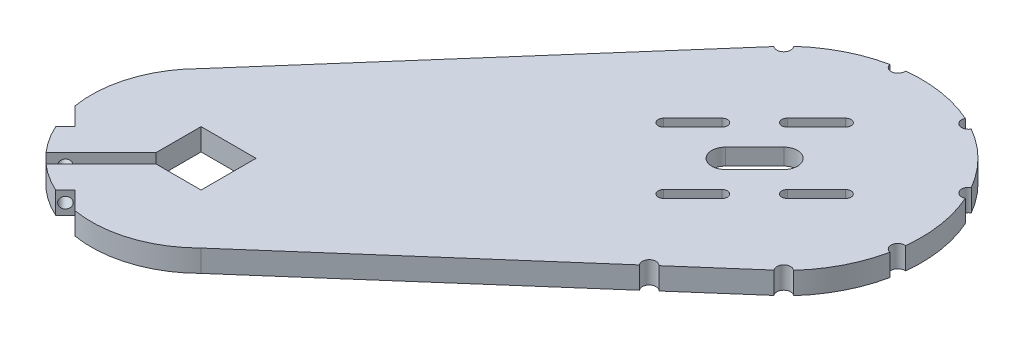
SolidWorks part; units mm, degrees
material "1060-H12"
ref_plane "Plan de face" through (0, 0, 0) normal (0, 0, 1) x (1, 0, 0)
ref_plane "Plan de dessus" through (0, 0, 0) normal (0, 1, 0) x (1, 0, 0)
ref_plane "Plan de droite" through (0, 0, 0) normal (1, 0, 0) x (0, 0, -1)
sketch "Esquisse1" plane through (0, 0, 0) normal (0, 1, 0) x (1, 0, 0)
  line L0 (0, 0) -> (106.066, 106.066) construction
  line L1 (-10, 10) -> (10, 10)
  line L2 (-10, 10) -> (-10, -10)
  line L3 (-10, -10) -> (10, -10)
  line L4 (10, 10) -> (10, -10)
  line L5 (-10, 10) -> (10, -10) construction
  line L6 (-10, -10) -> (10, 10) construction
  line L7 (106.066, 106.066) -> (141.4214, 70.7107) construction
  line L8 (0, 0) -> (28.2843, -28.2843) construction
  line L9 (28.2843, -28.2843) -> (141.4214, 70.7107)
  line L10 (-28.2843, 28.2843) -> (70.7107, 141.4214)
  arc A0 (70.7107, 141.4214) -> (141.4214, 70.7107) centre (106.066, 106.066) cw
  arc A1 (-28.2843, 28.2843) -> (28.2843, -28.2843) centre (0, 0) ccw
  dimension "D3" = 150
  dimension "D1" = 20
  dimension "D4" = 50
  dimension "D2" = 20
  dimension "D5" = 40
extrude "Boss.-Extru.1" add sketch "Esquisse1" along normal blind 8 contours L10 A1 L9 A0 L1 L4 L3 L2
sketch "Esquisse3" plane through (0, 8, 0) normal (0, 1, 0) x (1, 0, 0)
  line L0 (-10, -10) -> (-28.5289, -28.5289) construction
  line L3 (-8.2322, -11.7678) -> (-27.2344, -30.7699)
  line L4 (-27.2344, -30.7699) -> (-30.7699, -27.2344)
  line L5 (-30.7699, -27.2344) -> (-11.7678, -8.2322)
  line L6 (-11.7678, -8.2322) -> (-9.7269, -6.1913)
  line L7 (-9.7269, -6.1913) -> (-6.1913, -9.7269)
  line L8 (-6.1913, -9.7269) -> (-8.2322, -11.7678)
  line L9 (-8.2322, -11.7678) -> (-8.2082, -11.7266)
  point P3 (-19.2631, -19.2631)
  dimension "D1" = 13.1
  dimension "D2" = 2.5
  dimension "D3" = 2.5
extrude "Enlèv. mat.-Extru.1" cut sketch "Esquisse3" against normal through all
ref_plane "Plan1" through (0, 0, 0) normal (0.7071, 0, 0.7071) x (0.7071, 0, -0.7071)
sketch "Esquisse4" plane through (1.7678, 0, 1.7678) normal (-0.7071, 0, -0.7071) x (-0.7071, 0, 0.7071)
  line L0 (11.6421, 8) -> (39.9218, 8) construction
  line L1 (39.9218, 0) -> (39.9218, 8) construction
  circle A0 centre (34.9218, 4) radius 2
  point P0 (34.9218, 4)
  point P5 (39.9218, 4)
  dimension "D1" = 4
  dimension "D2" = 5
extrude "Enlèv. mat.-Extru.2" cut sketch "Esquisse4" against normal through all and the other way through all
sketch "Esquisse5" plane through (0, 8, 0) normal (0, 1, 0) x (1, 0, 0)
  line L0 (-29.9967, -26.4612) -> (-26.4612, -22.9257) construction
  line L1 (-29.9967, -26.4612) -> (-10, -6.4645) construction
  line L2 (-26.4612, -22.9257) -> (-41.741, -7.6459) construction
  line L3 (-34.6837, -14.7032) -> (-36.4514, -16.471)
  line L4 (-36.4514, -16.471) -> (-40.9085, -7.7776)
  line L5 (-40.9085, -7.7776) -> (-39.4911, -6.3602)
  line L6 (-39.4911, -6.3602) -> (-32.9159, -12.9355)
  line L7 (-32.9159, -12.9355) -> (-34.6837, -14.7032)
  line L8 (-28.8576, -28.8576) -> (-15.8397, -15.8397) construction
  line L9 (-3.1113, -3.1113) -> (3.1113, 3.1113) construction
  line L10 (-7.7776, -40.9085) -> (-6.3602, -39.4911)
  line L11 (-16.471, -36.4514) -> (-7.7776, -40.9085)
  line L12 (-14.7032, -34.6837) -> (-16.471, -36.4514)
  line L13 (-12.9355, -32.9159) -> (-14.7032, -34.6837)
  line L14 (-6.3602, -39.4911) -> (-12.9355, -32.9159)
  arc A0 (-28.2843, 28.2843) -> (-29.9967, -26.4612) centre (0, 0) ccw construction
  dimension "D1" = 5
  dimension "D2" = 2.5
  dimension "D3" = 2.5
extrude "Enlèv. mat.-Extru.3" cut sketch "Esquisse5" against normal through all
sketch "Esquisse7" plane through (0, 8, 0) normal (0, 1, 0) x (1, 0, 0)
  line L0 (0, 0) -> (106.066, 106.066) construction
  line L1 (106.066, 106.066) -> (141.4214, 70.7107) construction
  line L2 (10, 10) -> (106.066, 106.066) construction
  line L6 (106.066, 106.066) -> (109.6016, 109.6016) construction
  line L7 (95.4594, 95.4594) -> (66.5612, 95.4594) construction
  line L8 (95.4594, 95.4594) -> (106.066, 106.066) construction
  line L9 (91.9239, 98.9949) -> (102.5305, 109.6016)
  line L10 (98.9949, 91.9239) -> (109.6016, 102.5305)
  line L11 (106.066, 106.066) -> (106.066, 143.8436) construction
  line L12 (95.4594, 95.4594) -> (95.4594, 136.3981) construction
  line L13 (106.066, 106.066) -> (72.9746, 106.066) construction
  line L26 (95.4594, 117.9594) -> (106.066, 128.566) construction
  line L27 (94.0452, 119.3736) -> (104.6518, 129.9802)
  line L28 (96.8736, 116.5452) -> (107.4802, 127.1518)
  line L29 (72.9594, 95.4594) -> (83.566, 106.066) construction
  line L30 (71.5452, 96.8736) -> (82.1518, 107.4802)
  line L31 (74.3736, 94.0452) -> (84.9802, 104.6518)
  line L32 (117.9594, 95.4594) -> (128.566, 106.066) construction
  line L33 (119.3736, 94.0452) -> (129.9802, 104.6518)
  line L34 (116.5452, 96.8736) -> (127.1518, 107.4802)
  line L35 (95.4594, 72.9594) -> (106.066, 83.566) construction
  line L36 (96.8736, 71.5452) -> (107.4802, 82.1518)
  line L37 (94.0452, 74.3736) -> (104.6518, 84.9802)
  arc A0 (91.9239, 98.9949) -> (98.9949, 91.9239) centre (95.4594, 95.4594) ccw
  arc A1 (109.6016, 102.5305) -> (102.5305, 109.6016) centre (106.066, 106.066) ccw
  arc A10 (94.0452, 119.3736) -> (96.8736, 116.5452) centre (95.4594, 117.9594) ccw
  arc A11 (107.4802, 127.1518) -> (104.6518, 129.9802) centre (106.066, 128.566) ccw
  arc A12 (71.5452, 96.8736) -> (74.3736, 94.0452) centre (72.9594, 95.4594) ccw
  arc A13 (84.9802, 104.6518) -> (82.1518, 107.4802) centre (83.566, 106.066) ccw
  arc A14 (119.3736, 94.0452) -> (116.5452, 96.8736) centre (117.9594, 95.4594) cw
  arc A15 (127.1518, 107.4802) -> (129.9802, 104.6518) centre (128.566, 106.066) cw
  arc A16 (96.8736, 71.5452) -> (94.0452, 74.3736) centre (95.4594, 72.9594) cw
  arc A17 (104.6518, 84.9802) -> (107.4802, 82.1518) centre (106.066, 83.566) cw
  point P0 (106.066, 106.066)
  point P8 (95.4594, 95.4594)
  point P13 (100.7627, 100.7627)
  point P21 (106.066, 121.066)
  point P24 (95.4594, 110.4594)
  point P25 (91.066, 106.066)
  point P26 (80.4594, 95.4594)
  point P55 (106.066, 128.566)
  point P56 (95.4594, 117.9594)
  point P57 (83.566, 106.066)
  point P58 (72.9594, 95.4594)
  point P59 (100.7627, 123.2627)
  point P68 (78.2627, 100.7627)
  point P75 (123.2627, 100.7627)
  point P82 (100.7627, 78.2627)
  dimension "D4" = 45
  dimension "D11" = 15
  dimension "D1" = 5
  dimension "D2" = 15
  dimension "D3" = 45
  dimension "D5" = 45
  dimension "D6" = 45
  dimension "D7" = 15
  dimension "D8" = 15
  dimension "D9" = 15
  dimension "D10" = 15
  dimension "D12" = 22.5
  dimension "D13" = 22.5
  dimension "D14" = 22.5
  dimension "D15" = 22.5
extrude "Enlèv. mat.-Extru.4" cut sketch "Esquisse7" against normal through all
ref_plane "Plan2" through (0, 4, 0) normal (0, 1, 0) x (1, 0, 0)
sketch "Esquisse9" plane through (0, 0, 0) normal (0, -1, 0) x (-1, 0, 0)
  line L0 (-70.7107, 141.4214) -> (-106.066, 106.066) construction
  line L1 (0, 0) -> (-106.066, 106.066) construction
  line L2 (-155.4504, 98.2443) -> (-106.066, 106.066) construction
  line L4 (-106.066, 106.066) -> (-115.2875, 47.8436) construction
  line L5 (-106.066, 106.066) -> (-141.4214, 70.7107) construction
  line L6 (-28.2843, -28.2843) -> (-141.4214, 70.7107) construction
  circle A0 centre (-70.7107, 141.4214) radius 2.5
  circle A1 centre (-98.2443, 155.4504) radius 2.5
  circle A2 centre (-128.7655, 150.6163) radius 2.5
  circle A3 centre (-150.6163, 128.7655) radius 2.5
  circle A4 centre (-155.4504, 98.2443) radius 2.5
  circle A5 centre (-141.4214, 70.7107) radius 2.5
  circle A6 centre (-115.2875, 47.8436) radius 2.5
  point P19 (-106.066, 106.066)
  dimension "D2" = 6
  dimension "D3" = 36
  dimension "D1" = 50
extrude "Enlèv. mat.-Extru.6" cut sketch "Esquisse9" against normal through all
sketch "Esquisse11" plane through (0, 0, 0) normal (0, -1, 0) x (-1, 0, 0)
  line L0 (0, 0) -> (-106.066, 106.066) construction
  line L1 (-106.066, 106.066) -> (-95.4594, 95.4594) construction
  line L2 (-88.3883, 123.7437) -> (-77.7817, 113.1371)
  line L3 (-123.7437, 88.3883) -> (-113.1371, 77.7817)
  arc A0 (-102.5305, 109.6016) -> (-109.6016, 102.5305) centre (-106.066, 106.066) ccw construction
  arc A1 (-98.9949, 91.9239) -> (-91.9239, 98.9949) centre (-95.4594, 95.4594) ccw construction
  arc A2 (-88.3883, 123.7437) -> (-123.7437, 88.3883) centre (-106.066, 106.066) ccw
  arc A3 (-113.1371, 77.7817) -> (-77.7817, 113.1371) centre (-95.4594, 95.4594) ccw
  point P0 (-106.066, 106.066)
  point P7 (-109.6016, 109.6016)
  point P8 (-95.4594, 95.4594)
  point P13 (-100.7627, 100.7627)
  dimension "D1" = 5
  dimension "D2" = 0
extrude "Enlèv. mat.-Extru.8" cut sketch "Esquisse11" against normal blind 2
